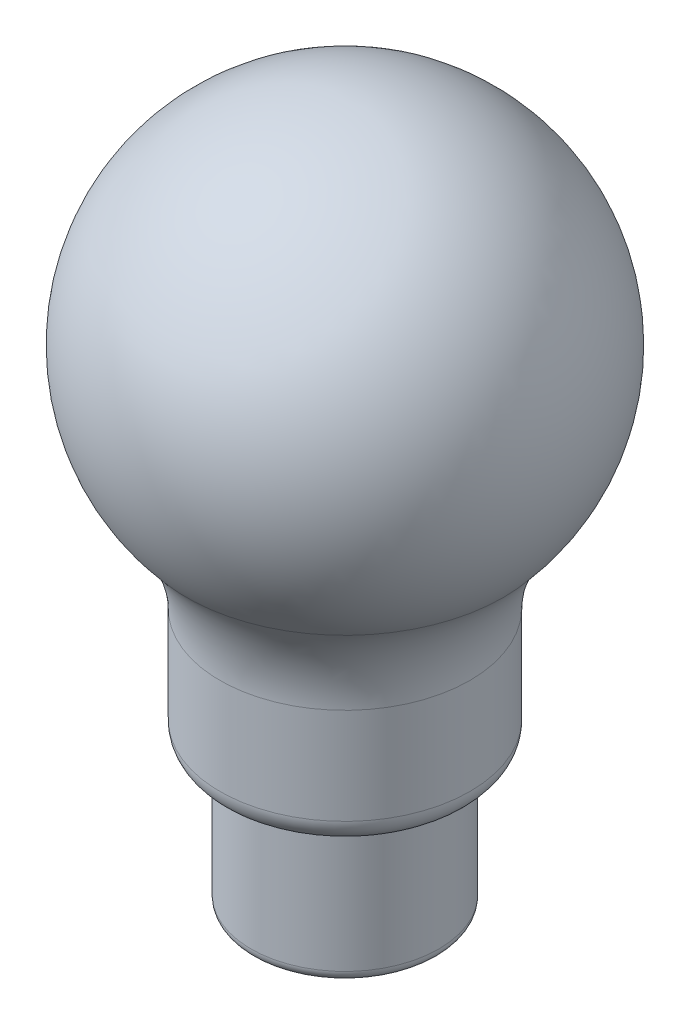
SolidWorks part; units mm, degrees
ref_plane "Front Plane" through (0, 0, 0) normal (0, 0, 1) x (1, 0, 0)
ref_plane "Top Plane" through (0, 0, 0) normal (0, 1, 0) x (1, 0, 0)
ref_plane "Right Plane" through (0, 0, 0) normal (1, 0, 0) x (0, 0, -1)
sketch "Sketch1" plane through (0, 0, 0) normal (0, 1, 0) x (1, 0, 0)
  circle A0 centre (7.5, 0) radius 0.5
  dimension "D1" = 1
  dimension "D2" = 7.5
sketch "Sketch2" plane through (0, 0, 0) normal (0, 0, 1) x (1, 0, 0)
  line L1 (8, 0) -> (7, 0) construction
  spline S0 degree 2 poles (7.5, 0) (7.0697, 25.0113) (8.3347, 50) knots 0 0 0 1 1 1
  dimension "D1" = 20
  dimension "D2" = 50
sweep "Sweep1" add profiles "Sketch1" path "Sketch2"
sketch "Sketch3" plane through (0, 0, 0) normal (0, 1, 0) x (1, 0, 0)
  circle A0 centre (-7.5, 0) radius 0.5
  dimension "D1" = 1
  dimension "D2" = 7.5
sketch "Sketch4" plane through (0, 0, 0) normal (0, 0, 1) x (1, 0, 0)
  line L1 (-7, 0) -> (-8, 0) construction
  spline S0 degree 2 poles (-7.5, 0) (-7.3334, 25.0035) (-8, 50) knots 0 0 0 1 1 1
  dimension "D1" = 20
  dimension "D2" = 50
sweep "Sweep2" add profiles "Sketch3" path "Sketch4"
sketch "Sketch5" plane through (0, 0, 0) normal (1, 0, 0) x (0, 0, -1)
  circle A0 centre (0.074, 49) radius 0.125
  ellipse E0 centre (0, 50) end of major axis (0.5, 50) minor radius 0.0339 construction
  dimension "D1" = 0.25
  dimension "D2" = 1
extrude "Cut-Extrude1" cut sketch "Sketch5" against normal through all and the other way through all
sketch "Sketch6" plane through (0, 0, 0) normal (0, 0, 1) x (1, 0, 0)
  line L0 (0, 90.6) -> (0, 90)
  line L1 (-12, -10) -> (-12, -10.6)
  line L2 (-17.5, 26.9281) -> (-17.5, 13)
  line L3 (-14.5, 10) -> (-14, 10)
  line L6 (-18.1, 26.9281) -> (-18.1, 13)
  line L7 (-13, 9) -> (-13, -9)
  line L9 (-14.5, 9.4) -> (-14, 9.4)
  line L10 (-13.6, 9) -> (-13.6, -9)
  line L12 (-12, -10.6) -> (0, -10.6) construction
  line L13 (-12, -10) -> (0, -10) construction
  arc A0 (0, 90) -> (-22.5, 40.1569) centre (0, 60) ccw
  arc A1 (0, 90.6) -> (-22.95, 39.76) centre (0, 60) ccw
  arc A2 (-17.5, 26.9281) -> (-22.5, 40.1569) centre (-37.5, 26.9281) ccw
  arc A3 (-18.1, 26.9281) -> (-22.95, 39.76) centre (-37.5, 26.9281) ccw
  arc A4 (-14.5, 10) -> (-17.5, 13) centre (-14.5, 13) cw
  arc A5 (-14.5, 9.4) -> (-18.1, 13) centre (-14.5, 13) cw
  arc A6 (-12, -10) -> (-13, -9) centre (-12, -9) cw
  arc A7 (-13.6, 9) -> (-14, 9.4) centre (-14, 9) ccw
  arc A8 (-13, 9) -> (-14, 10) centre (-14, 9) ccw
  arc A9 (-12, -10.6) -> (-13.6, -9) centre (-12, -9) cw
  point P17 (17.5, 10)
  point P20 (-17.5, 10)
  point P23 (13, -10)
  point P26 (-13, -10)
  point P29 (13, 10)
  dimension "D1" = 60
  dimension "D7" = 0.6
  dimension "D2" = 60
  dimension "D3" = 35
  dimension "D4" = 50
  dimension "D5" = 26
sketch "Sketch7" plane through (0, 0, 0) normal (0, 0, 1) x (1, 0, 0)
  line L0 (0, -10.6) -> (0, 90.6) construction
revolve "Revolve2" add sketch "Sketch6" angle 360 about L0
